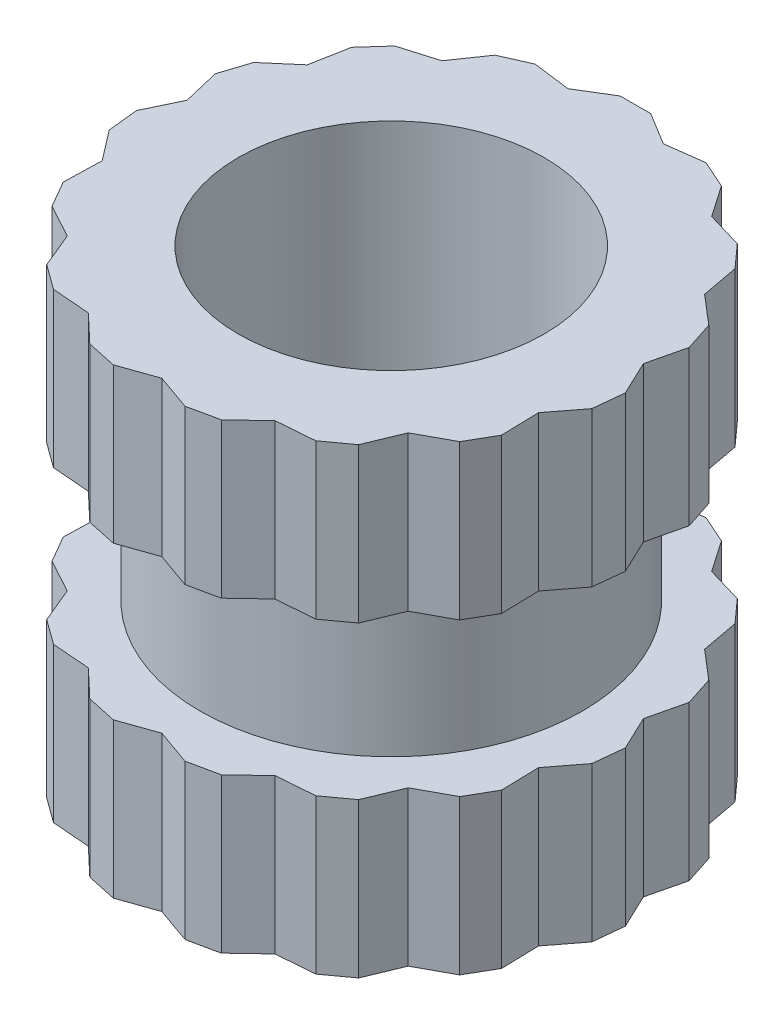
SolidWorks part; units mm, degrees
ref_plane "Front Plane" through (0, 0, 0) normal (0, 0, 1) x (1, 0, 0)
ref_plane "Top Plane" through (0, 0, 0) normal (0, 1, 0) x (1, 0, 0)
ref_plane "Right Plane" through (0, 0, 0) normal (1, 0, 0) x (0, 0, -1)
sketch "Sketch1" plane through (0, 0, 0) normal (0, 1, 0) x (1, 0, 0)
  circle A0 centre (0, 0) radius 1.25
  circle A1 centre (0, 0) radius 1
  dimension "D1" = 2.5
  dimension "D2" = 2
extrude "Boss-Extrude1" add sketch "Sketch1" along normal blind 0.5
sketch "Sketch2" plane through (0, 0.5, 0) normal (0, 1, 0) x (1, 0, 0)
  line L0 (0, 0) -> (0, 1.6) construction
  line L1 (0, 0) -> (-0.3327, 1.565) construction
  line L2 (-0.3119, 1.4672) -> (-0.1, 1.5969)
  line L3 (-0.1, 1.5969) -> (0.1, 1.5969)
  line L4 (0.3119, 1.4672) -> (0.5582, 1.4995)
  line L5 (0.3119, 1.4672) -> (0.1, 1.5969)
  line L6 (0.5582, 1.4995) -> (0.7409, 1.4181)
  line L7 (0.8817, 1.2135) -> (0.7409, 1.4181)
  line L8 (0.8817, 1.2135) -> (1.1198, 1.1428)
  line L9 (1.1198, 1.1428) -> (1.2536, 0.9942)
  line L10 (1.299, 0.75) -> (1.2536, 0.9942)
  line L11 (1.299, 0.75) -> (1.4878, 0.5886)
  line L12 (1.4878, 0.5886) -> (1.5496, 0.3984)
  line L13 (1.4918, 0.1568) -> (1.5496, 0.3984)
  line L14 (1.4918, 0.1568) -> (1.5986, -0.0675)
  line L15 (1.5986, -0.0675) -> (1.5777, -0.2664)
  line L16 (1.4266, -0.4635) -> (1.5777, -0.2664)
  line L17 (1.4266, -0.4635) -> (1.4329, -0.7118)
  line L18 (1.4329, -0.7118) -> (1.3329, -0.885)
  line L19 (1.1147, -1.0037) -> (1.3329, -0.885)
  line L20 (1.1147, -1.0037) -> (1.0195, -1.2331)
  line L21 (1.0195, -1.2331) -> (0.8577, -1.3507)
  line L22 (0.6101, -1.3703) -> (0.8577, -1.3507)
  line L23 (0.6101, -1.3703) -> (0.4298, -1.5412)
  line L24 (0.4298, -1.5412) -> (0.2342, -1.5828)
  line L25 (0, -1.5) -> (0.2342, -1.5828)
  line L26 (0, -1.5) -> (-0.2342, -1.5828)
  line L27 (-0.2342, -1.5828) -> (-0.4298, -1.5412)
  line L28 (-0.6101, -1.3703) -> (-0.4298, -1.5412)
  line L29 (-0.6101, -1.3703) -> (-0.8577, -1.3507)
  line L30 (-0.8577, -1.3507) -> (-1.0195, -1.2331)
  line L31 (-1.1147, -1.0037) -> (-1.0195, -1.2331)
  line L32 (-1.1147, -1.0037) -> (-1.3329, -0.885)
  line L33 (-1.3329, -0.885) -> (-1.4329, -0.7118)
  line L34 (-1.4266, -0.4635) -> (-1.4329, -0.7118)
  line L35 (-1.4266, -0.4635) -> (-1.5777, -0.2664)
  line L36 (-1.5777, -0.2664) -> (-1.5986, -0.0675)
  line L37 (-1.4918, 0.1568) -> (-1.5986, -0.0675)
  line L38 (-1.4918, 0.1568) -> (-1.5496, 0.3984)
  line L39 (-1.5496, 0.3984) -> (-1.4878, 0.5886)
  line L40 (-1.299, 0.75) -> (-1.4878, 0.5886)
  line L41 (-1.299, 0.75) -> (-1.2536, 0.9942)
  line L42 (-1.2536, 0.9942) -> (-1.1198, 1.1428)
  line L43 (-0.8817, 1.2135) -> (-1.1198, 1.1428)
  line L44 (-0.8817, 1.2135) -> (-0.7409, 1.4181)
  line L45 (-0.7409, 1.4181) -> (-0.5582, 1.4995)
  line L46 (-0.3119, 1.4672) -> (-0.5582, 1.4995)
  circle A22 centre (0, 0) radius 1 construction
  circle A23 centre (0, 0) radius 1
  circle A24 centre (0, 0) radius 1.6
  circle A25 centre (0, 0) radius 1.5
  point P69 (0, 0)
  dimension "D1" = 3.2
  dimension "D2" = 3
  dimension "D3" = 12
  dimension "D4" = 0.2
extrude "Boss-Extrude2" add sketch "Sketch2" along normal blind 1.01
mirror "Mirror1" about plane through (0, 0, 0) normal (0, 1, 0) of "Boss-Extrude1", "Boss-Extrude2"
